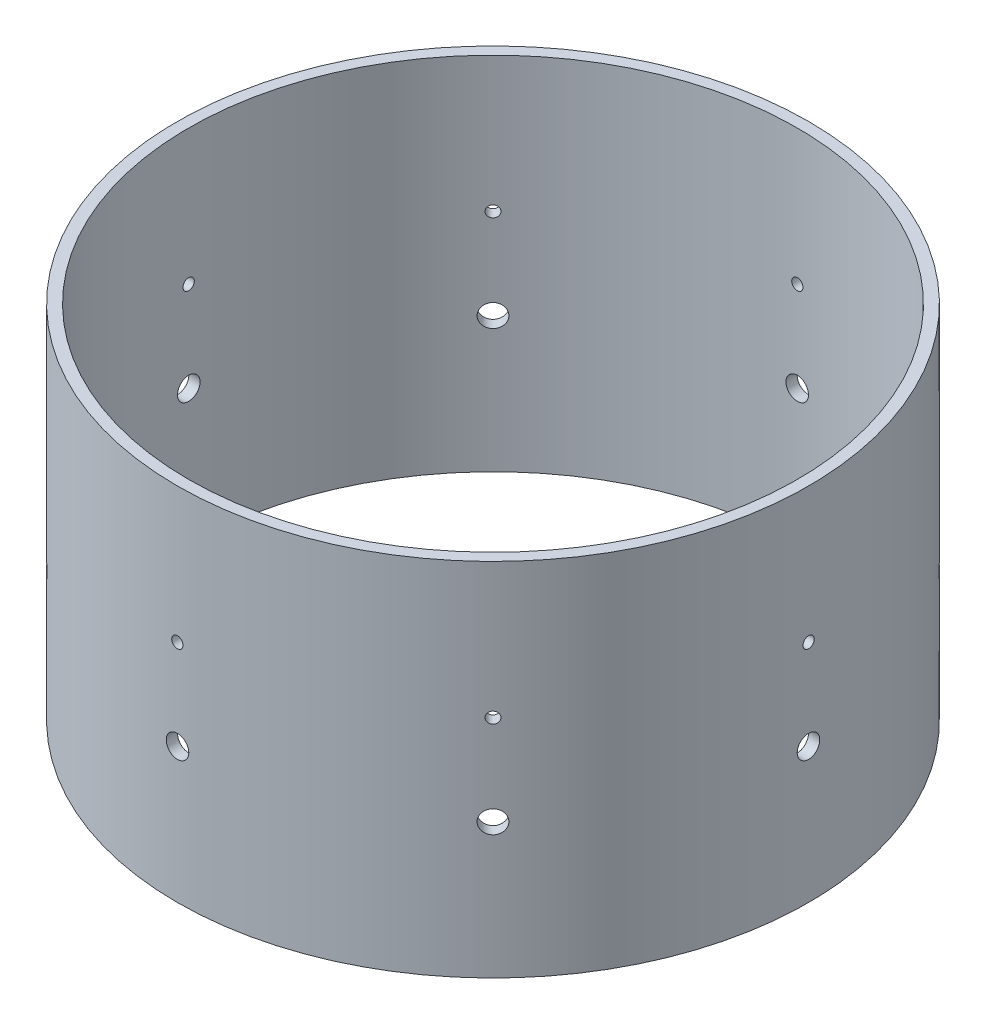
SolidWorks part; units mm, degrees
ref_plane "Front Plane" through (0, 0, 0) normal (0, 0, 1) x (1, 0, 0)
ref_plane "Top Plane" through (0, 0, 0) normal (0, 1, 0) x (1, 0, 0)
ref_plane "Right Plane" through (0, 0, 0) normal (1, 0, 0) x (0, 0, -1)
sketch "Sketch1" plane through (0, 0, 0) normal (0, 1, 0) x (1, 0, 0)
  circle A0 centre (0, 0) radius 88.9
  circle A1 centre (0, 0) radius 85.725
  dimension "D1" = 177.8
  dimension "D2" = 171.45
extrude "Boss-Extrude1" add sketch "Sketch1" along normal blind 101.6
sketch "Sketch2" plane through (0, 0, 0) normal (0, 0, 1) x (1, 0, 0)
  line L0 (0, 0) -> (0, 101.6) construction
  line L1 (85.725, 101.6) -> (-85.725, 101.6) construction
  line L2 (-88.9, 0) -> (88.9, 0) construction
  circle A0 centre (0, 63.5) radius 1.5875
  circle A1 centre (0, 38.1) radius 3.175
  dimension "D1" = 3.175
  dimension "D2" = 6.35
  dimension "D3" = 38.1
  dimension "D4" = 38.1
extrude "Cut-Extrude1" cut sketch "Sketch2" against normal through all
pattern_circular "CirPattern1" count 8 over 360 about axis through (0, 0, 0) along (0, 1, 0) of "Cut-Extrude1"
